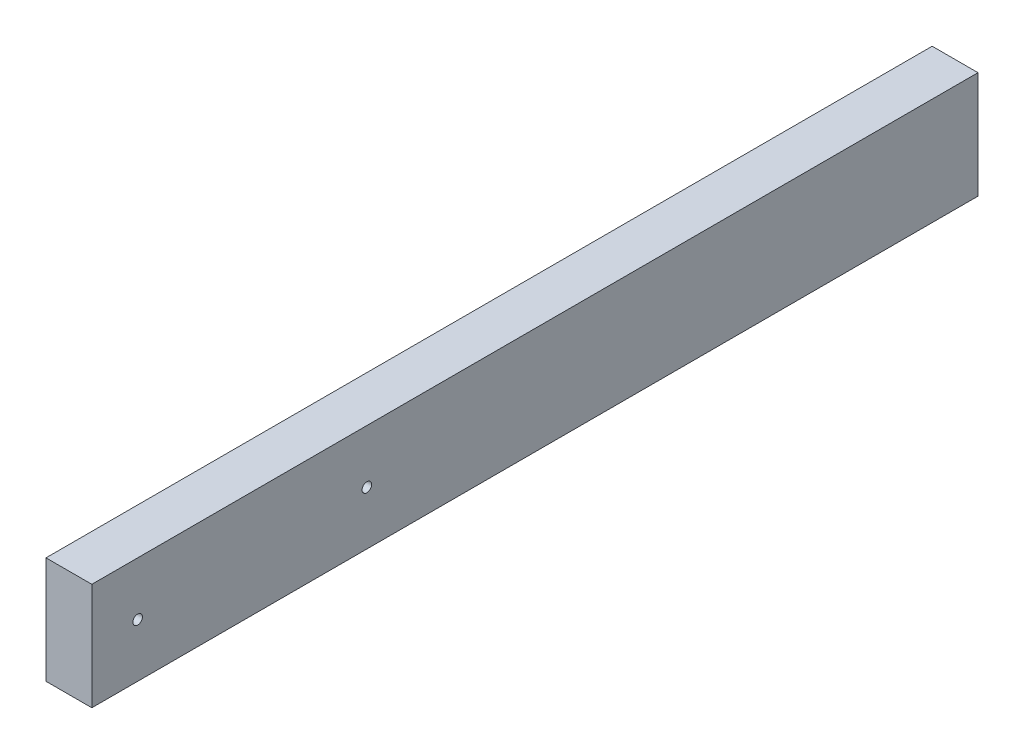
SolidWorks part; units mm, degrees
material "Pine"
ref_plane "Front Plane" through (0, 0, 0) normal (0, 0, 1) x (1, 0, 0)
ref_plane "Top Plane" through (0, 0, 0) normal (0, 1, 0) x (1, 0, 0)
ref_plane "Right Plane" through (0, 0, 0) normal (1, 0, 0) x (0, 0, -1)
sketch "Sketch1" plane through (0, 0, 0) normal (0, 0, 1) x (1, 0, 0)
  line L1 (-19.05, -44.45) -> (19.05, -44.45)
  line L2 (-19.05, -44.45) -> (-19.05, 44.45)
  line L3 (-19.05, 44.45) -> (19.05, 44.45)
  line L4 (19.05, -44.45) -> (19.05, 44.45)
  line L5 (-19.05, -44.45) -> (19.05, 44.45) construction
  line L6 (-19.05, 44.45) -> (19.05, -44.45) construction
  point P0 (0, 0)
  dimension "D1" = 88.9
  dimension "D2" = 38.1
extrude "Boss-Extrude1" add sketch "Sketch1" along normal blind 736.6
sketch "Sketch2" plane through (19.05, 0, 0) normal (1, 0, 0) x (0, 0, -1)
  line L0 (-736.6, -44.45) -> (-736.6, 44.45) construction
  point P0 (-698.5, 0)
  point P1 (-508, 0)
  dimension "D1" = 38.1
  dimension "D2" = 190.5
hole_wizard "5/16 (0.3125) Diameter Hole1" positions "Sketch3" profile "Sketch4" hole size "5/16" standard "ANSI Inch" end condition through all
sketch "Sketch3" plane through (19.05, 0, 0) normal (1, 0, 0) x (0, 0, -1)
  point P0 (-698.5, 0)
  point P3 (-508, 0)
sketch "Sketch4" plane through (19.05, 0, 698.5) normal (0, 1, 0) x (0, 0, -1)
  line L0 (0, 0) -> (0, 38.1)
  line L1 (0, 38.1) -> (3.9687, 38.1)
  line L2 (3.9687, 38.1) -> (3.9687, 0)
  line L5 (3.9687, 0) -> (0, 0)
  line L11 (0, -6.35) -> (0, 107.95) construction
  dimension "Thru Hole Dia." = 7.9375
  dimension "Thru Hole Depth" = 38.1
